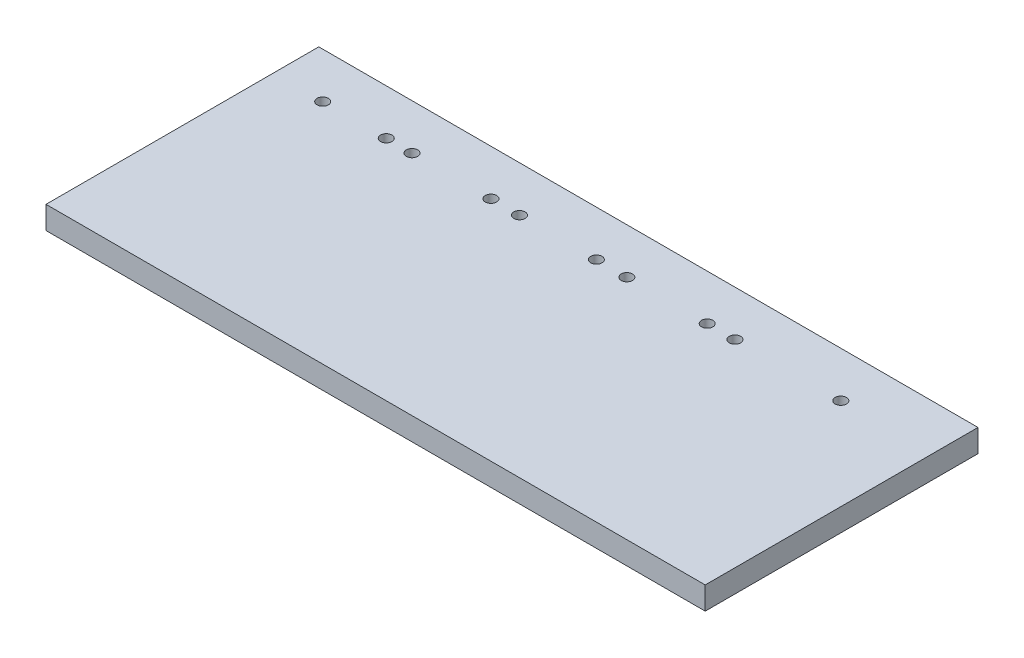
SolidWorks part; units mm, degrees
ref_plane "Спереди" through (0, 0, 0) normal (0, 0, 1) x (1, 0, 0)
ref_plane "Сверху" through (0, 0, 0) normal (0, 1, 0) x (1, 0, 0)
ref_plane "Справа" through (0, 0, 0) normal (1, 0, 0) x (0, 0, -1)
sketch "Эскиз1" plane through (0, 0, 0) normal (0, 1, 0) x (1, 0, 0)
  line L1 (0, 0) -> (290, 0)
  line L2 (0, 0) -> (0, 120)
  line L3 (0, 120) -> (290, 120)
  line L4 (290, 0) -> (290, 120)
extrude "Бобышка-Вытянуть1" add sketch "Эскиз1" along normal blind 10
sketch "Эскиз2" plane through (0, 10, 0) normal (0, 1, 0) x (1, 0, 0)
  line L0 (-12.5, 100) -> (291.5, 100) construction
  circle A4 centre (203.0595, 100) radius 2.5
  circle A6 centre (155.5438, 100) radius 2.5
  circle A8 centre (108.2766, 100) radius 2.5
  circle A9 centre (61.0095, 100) radius 2.5
  circle A12 centre (21.729, 100) radius 2.5
  circle A13 centre (49.6835, 100) radius 2.5
  circle A15 centre (95.7425, 100) radius 2.5
  circle A17 centre (142.1036, 100) radius 2.5
  circle A19 centre (190.8809, 100) radius 2.5
  circle A21 centre (249.6556, 100) radius 2.5
extrude "Вырез-Вытянуть1" cut sketch "Эскиз2" against normal through all
